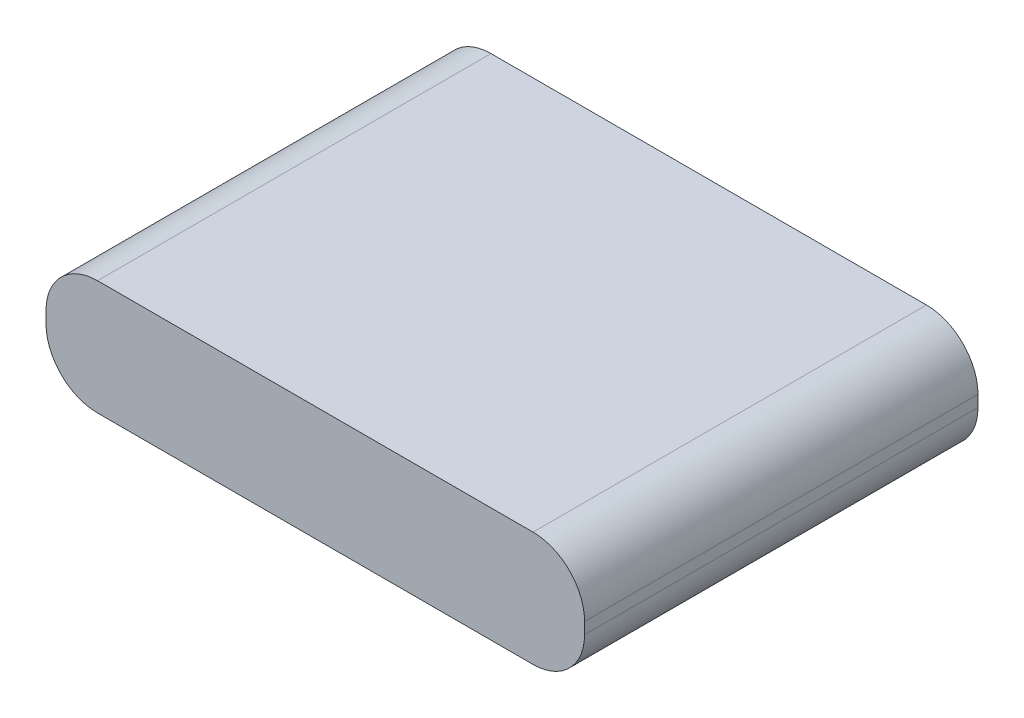
SolidWorks part; units mm, degrees
ref_plane "Front Plane" through (0, 0, 0) normal (0, 0, 1) x (1, 0, 0)
ref_plane "Top Plane" through (0, 0, 0) normal (0, 1, 0) x (1, 0, 0)
ref_plane "Right Plane" through (0, 0, 0) normal (1, 0, 0) x (0, 0, -1)
sketch "Sketch1" plane through (0, 0, 0) normal (0, 1, 0) x (1, 0, 0)
  line L1 (-35.25, -25.75) -> (35.25, -25.75)
  line L2 (-35.25, -25.75) -> (-35.25, 25.75)
  line L3 (-35.25, 25.75) -> (35.25, 25.75)
  line L4 (35.25, -25.75) -> (35.25, 25.75)
  line L5 (-35.25, -25.75) -> (35.25, 25.75) construction
  line L6 (-35.25, 25.75) -> (35.25, -25.75) construction
  point P0 (0, 0)
  dimension "D1" = 51.5
  dimension "D2" = 70.5
extrude "Boss-Extrude1" add sketch "Sketch1" along normal blind 15
fillet "Fillet1" radius 6.75 4 edges at (-35.25, 0, 0) (-35.25, 15, 0) (35.25, 0, 0) (35.25, 15, 0)
